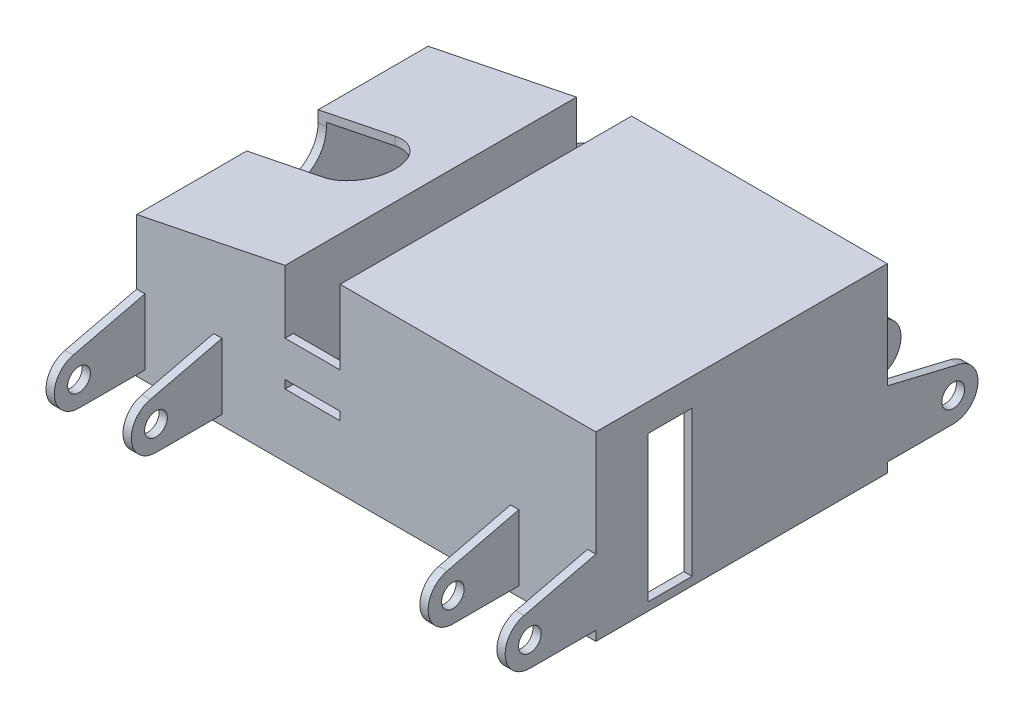
SolidWorks part; units mm, degrees
material "AISI 1020"
ref_plane "Front Plane" through (0, 0, 0) normal (0, 0, 1) x (1, 0, 0)
ref_plane "Top Plane" through (0, 0, 0) normal (0, 1, 0) x (1, 0, 0)
ref_plane "Right Plane" through (0, 0, 0) normal (1, 0, 0) x (0, 0, -1)
sketch "Sketch1" plane through (0, 0, 0) normal (0, 0, 1) x (1, 0, 0)
  line L0 (0, 60) -> (0, -3)
  line L1 (3, -3) -> (0, -3)
  line L2 (3, 63) -> (3, -3)
  line L3 (-87, 60) -> (-87, -3)
  line L4 (-87, -3) -> (-90, -3)
  line L5 (-90, -3) -> (-90, 17)
  line L6 (-90, 20) -> (-110.0009, 20)
  line L7 (-161, 45.5471) -> (-161, -3)
  line L8 (-113, 17) -> (-90, 17)
  line L9 (-161, -3) -> (-164, -3)
  line L11 (-110.0331, 58.9392) -> (-110.0009, 20)
  line L12 (-110.0331, 58.9392) -> (-164, 48)
  line L14 (-113, 55.2768) -> (-161, 45.5471)
  line L15 (-164, -3) -> (-164, 48)
  line L62 (-90, 63) -> (-90, 20)
  line L134 (-113, 55.2768) -> (-113, 17)
  line L139 (-87, 60) -> (0, 60)
  line L143 (3, 63) -> (-90, 63)
extrude "Boss-Extrude1" add sketch "Sketch1" along normal blind 100
sketch "Sketch2" plane through (0, 0, 100) normal (0, 0, 1) x (1, 0, 0)
  line L18 (-164, -3) -> (3, -3)
  line L19 (-164, 48) -> (-110.0331, 58.9392)
  line L21 (-110.0009, 20) -> (-110.0331, 58.9392) construction
  line L22 (-110.0141, 36) -> (-90, 36)
  line L23 (-90, 63) -> (-90, 20) construction
  line L24 (-90, 36) -> (-90, 63)
  line L25 (-110.0331, 58.9392) -> (-110.0141, 36)
  line L36 (3, 63) -> (-90, 63)
  line L37 (-90, 63) -> (-90, 20)
  line L38 (-90, 20) -> (-110.0009, 20)
  line L39 (-110.0009, 20) -> (-110.0331, 58.9392)
  line L40 (-110.0331, 58.9392) -> (-164, 48)
  line L41 (-164, 48) -> (-164, -3)
  line L42 (-164, -3) -> (-161, -3)
  line L43 (-161, -3) -> (-161, 45.5471)
  line L44 (-161, 45.5471) -> (-113, 55.2768)
  line L45 (-113, 55.2768) -> (-113, 17)
  line L46 (-113, 17) -> (-90, 17)
  line L47 (-90, 17) -> (-90, -3)
  line L48 (-90, -3) -> (-87, -3)
  line L49 (-87, -3) -> (-87, 60)
  line L50 (-87, 60) -> (0, 60)
  line L51 (0, 60) -> (0, -3)
  line L52 (0, -3) -> (3, -3)
  line L53 (3, -3) -> (3, 63)
  line L54 (3, 63) -> (-90, 63)
  line L59 (-164, 48) -> (-164, -3)
  line L71 (3, -3) -> (3, 63)
  dimension "D1" = 0
extrude "Boss-Extrude2" add sketch "Sketch2" along normal blind 3
sketch "Sketch4" plane through (0, -3, 0) normal (0, -1, 0) x (1, 0, 0)
  line L0 (-90, 69) -> (-90, 100) construction
  line L7 (-90, 100) -> (-90, 0) construction
  line L8 (-90, 69) -> (-161, 69)
  line L9 (-161, 100) -> (-161, 0) construction
  line L10 (-161, 69) -> (-161, 66)
  line L11 (-161, 66) -> (-90, 66)
  line L12 (-90, 100) -> (-90, 0) construction
  line L13 (-90, 66) -> (-90, 69)
  dimension "D1" = 31
  dimension "D2" = 3
extrude "Boss-Extrude3" add sketch "Sketch4" against normal up to surface (20 mm away) up to face at (-101.5, 17, 50)
sketch "Sketch6" plane through (0, 17, 0) normal (0, 1, 0) x (1, 0, 0)
  line L0 (-113, -69) -> (-113, -66)
  line L1 (-113, -66) -> (-161, -66)
  line L2 (-161, -66) -> (-113, -66) construction
  line L3 (-161, -66) -> (-161, -69)
  line L4 (-161, -69) -> (-113, -69)
extrude "Boss-Extrude4" add sketch "Sketch6" along normal up to surface (28.5471 mm away)
sketch "Sketch7" plane through (-164, 0, 0) normal (-1, 0, 0) x (0, 0, 1)
  line L0 (50, 48) -> (50, 44) construction
  line L1 (103, 48) -> (0, 48) construction
  line L5 (103, 48) -> (63, 48) construction
  line L6 (51.5, 48) -> (50, 48) construction
  line L7 (37, 44) -> (37, 57)
  line L8 (37, 57) -> (63, 57)
  line L9 (63, 57) -> (63, 44)
  line L10 (62.3693, 48) -> (51.5, 48) construction
  arc A1 (37, 44) -> (63, 44) centre (50, 44) ccw
extrude "Cut-Extrude1" cut sketch "Sketch7" against normal blind 3
sketch "Sketch8" plane through (0, 0, 66) normal (0, 0, -1) x (-1, 0, 0)
  line L0 (161, -3) -> (136, -3) construction
  line L1 (161, -3) -> (90, -3) construction
  line L2 (136, -3) -> (136, 22) construction
  line L3 (136, 22) -> (151.5, 22) construction
  line L4 (151.5, 22) -> (151.5, 37.5) construction
  line L5 (151.5, 22) -> (151.5, 6.5) construction
  line L6 (136, 22) -> (120.5, 22) construction
  line L7 (120.5, 22) -> (120.5, 37.5) construction
  line L8 (120.5, 22) -> (120.5, 6.5) construction
  circle A0 centre (136, 22) radius 2.5
  circle A1 centre (151.5, 37.5) radius 1.7
  circle A2 centre (120.5, 37.5) radius 1.7
  circle A3 centre (151.5, 6.5) radius 1.7
  circle A4 centre (120.5, 6.5) radius 1.7
extrude "Cut-Extrude2" cut sketch "Sketch8" against normal blind 3
sketch "Sketch9" plane through (-87, 0, 0) normal (1, 0, 0) x (0, 0, -1)
  line L0 (0, -3) -> (-31, -3) construction
  line L1 (-100, -3) -> (0, -3) construction
  line L2 (-31, -3) -> (-31, 29.5) construction
  line L3 (-31, 29.5) -> (-7.43, 29.5) construction
  line L4 (-7.43, 29.5) -> (-7.43, 5.93) construction
  line L5 (-7.43, 29.5) -> (-7.43, 53.07) construction
  line L6 (-31, 29.5) -> (-54.57, 29.5) construction
  line L7 (-54.57, 29.5) -> (-54.57, 53.07) construction
  line L8 (-54.57, 29.5) -> (-54.57, 5.93) construction
  circle A0 centre (-31, 29.5) radius 3.2
  circle A1 centre (-7.43, 53.07) radius 2.5
  circle A2 centre (-7.43, 5.93) radius 2.5
  circle A3 centre (-54.57, 53.07) radius 2.5
  circle A4 centre (-54.57, 5.93) radius 2.5
  dimension "D1" = 32.5
extrude "Cut-Extrude3" cut sketch "Sketch9" against normal blind 3
sketch "Sketch10" plane through (0, 0, 66) normal (0, 0, -1) x (-1, 0, 0)
  circle A0 centre (99.5, 6.5) radius 1.7
extrude "Cut-Extrude4" cut sketch "Sketch10" against normal blind 3
sketch "Sketch13" plane through (-90, 0, 0) normal (-1, 0, 0) x (0, 0, 1)
  line L0 (78.5, 6.43) -> (78.5, -3) construction
  line L1 (100, -3) -> (0, -3) construction
  line L2 (78.5, 6.43) -> (94.5, 6.43) construction
  circle A0 centre (94.5, 6.43) radius 2.5
extrude "Cut-Extrude6" cut sketch "Sketch13" against normal blind 3
sketch "Sketch14" plane through (0, 0, 0) normal (0, 0, -1) x (-1, 0, 0)
  line L0 (-3, 63) -> (-3, -3)
  line L1 (-3, -3) -> (164, -3)
  line L2 (164, -3) -> (164, 48)
  line L3 (164, 48) -> (110.0331, 58.9392)
  line L4 (110.0331, 58.9392) -> (110.0141, 36)
  line L5 (110.0141, 36) -> (90, 36)
  line L6 (90, 36) -> (90, 63)
  line L7 (90, 63) -> (-3, 63)
extrude "Boss-Extrude5" add sketch "Sketch14" along normal blind 3
sketch "Sketch15" plane through (0, -3, 0) normal (0, -1, 0) x (1, 0, 0)
  line L0 (-161, 100) -> (-159, 100) construction
  line L1 (-161, 100) -> (-113, 100) construction
  line L2 (-159, 100) -> (-159, 98) construction
  line L3 (-154, 98) -> (-154, 100)
  line L4 (-161, 100) -> (-90, 100) construction
  line L5 (-159, 93) -> (-161, 93)
  line L6 (-161, 100) -> (-161, 69) construction
  line L7 (-161, 93) -> (-161, 100)
  line L8 (-161, 100) -> (-154, 100)
  line L9 (0, 100) -> (-2, 100) construction
  line L10 (-87, 100) -> (0, 100) construction
  line L11 (-2, 100) -> (-2, 98) construction
  line L12 (-7, 98) -> (-7, 100)
  line L13 (-2, 93) -> (0, 93)
  line L14 (0, 100) -> (0, 0) construction
  line L15 (-7, 100) -> (0, 100)
  line L16 (0, 100) -> (0, 93)
  line L17 (-161, 0) -> (-159, 0) construction
  line L18 (-161, 0) -> (-113, 0) construction
  line L19 (-159, 0) -> (-159, 2) construction
  line L20 (-159, 7) -> (-161, 7)
  line L21 (-161, 66) -> (-161, 0) construction
  line L22 (-154, 2) -> (-154, 0)
  line L23 (-90, 0) -> (-161, 0) construction
  line L24 (-161, 7) -> (-161, 0)
  line L25 (-161, 0) -> (-154, 0)
  line L26 (0, 0) -> (-2, 0) construction
  line L27 (-87, 0) -> (0, 0) construction
  line L28 (-2, 0) -> (-2, 2) construction
  line L29 (-7, 2) -> (-7, 0)
  line L30 (-2, 7) -> (0, 7)
  line L31 (0, 100) -> (0, 0) construction
  line L32 (0, 7) -> (0, 0)
  line L33 (0, 0) -> (-7, 0)
  circle A0 centre (-159, 98) radius 2
  arc A1 (-159, 93) -> (-154, 98) centre (-159, 98) ccw
  circle A2 centre (-159, 98) radius 5 construction
  circle A3 centre (-2, 98) radius 2
  arc A4 (-7, 98) -> (-2, 93) centre (-2, 98) ccw
  circle A5 centre (-2, 98) radius 5 construction
  circle A6 centre (-159, 2) radius 2
  arc A7 (-154, 2) -> (-159, 7) centre (-159, 2) ccw
  circle A8 centre (-159, 2) radius 5 construction
  circle A9 centre (-2, 2) radius 2
  arc A10 (-2, 7) -> (-7, 2) centre (-2, 2) ccw
  circle A11 centre (-2, 2) radius 5 construction
  line M15 (0, 0) -> (-87, 0)
  line M17 (-87, 100) -> (0, 100)
  line M18 (0, 100) -> (0, 0)
  line M19 (-161, 0) -> (-161, 66)
  line M22 (-90, 0) -> (-161, 0)
  line M24 (-161, 69) -> (-161, 100)
  line M25 (-161, 100) -> (-90, 100)
  dimension "D1" = 3
  dimension "D2" = 3
  dimension "D3" = 3
  dimension "D4" = 3
extrude "Boss-Extrude6" add sketch "Sketch15" against normal blind 5 contours L5 A1 L3 L8 A0 M24 | A0 L7 M25 | L12 A4 L13 L16 A3 M17 | A3 L15 M18 | L30 A10 L29 L33 A9 M18 | A9 L32 M15 | L22 A7 L20 L24 A6 M22 | A6 L25 M19
sketch "Sketch19" plane through (0, 63, 0) normal (0, 1, 0) x (1, 0, 0)
  line L0 (-161, -50) -> (-136, -50) construction
  line L1 (-161, -63) -> (-161, -37) construction
  line L2 (-136, -37) -> (-164, -37)
  line L3 (-164, -37) -> (-164, -63)
  line L4 (-164, -63) -> (-136, -63)
  arc A0 (-136, -63) -> (-136, -37) centre (-136, -50) ccw
extrude "Cut-Extrude8" cut sketch "Sketch19" against normal blind 18
sketch "Sketch20" plane through (0, 0, 100) normal (0, 0, -1) x (-1, 0, 0)
  line L0 (90, 36) -> (90, 20) construction
  line L1 (110.0009, 20) -> (90, 20)
  line L2 (110.0009, 20) -> (110.0009, 23)
  line L3 (110.0009, 23) -> (90, 23)
  line L4 (90, 20) -> (90, 23)
  dimension "D1" = 3
extrude "Cut-Extrude9" cut sketch "Sketch20" against normal blind 3
sketch "Sketch21" plane through (0, 0, 0) normal (0, 0, 1) x (1, 0, 0)
  line L0 (-90, 36) -> (-90, 20) construction
  line L1 (-110.0009, 20) -> (-90, 20)
  line L2 (-110.0009, 20) -> (-110.0009, 23)
  line L3 (-110.0009, 23) -> (-90, 23)
  line L4 (-90, 20) -> (-90, 23)
  dimension "D1" = 3
extrude "Cut-Extrude10" cut sketch "Sketch21" against normal blind 3
sketch "Sketch22" plane through (-164, 0, 0) normal (-1, 0, 0) x (0, 0, 1)
  line L0 (103, -3) -> (103, 9.5) construction
  line L1 (103, 48) -> (103, -3) construction
  line L2 (103, 0.5) -> (103, 24.5)
  line L3 (127, 0.5) -> (103, 0.5)
  line L4 (103, 24.5) -> (129.0954, 18.2527)
  line L5 (50, -3) -> (50, 28.093) construction
  line L6 (103, -3) -> (-3, -3) construction
  line L7 (-3, -3) -> (-3, 9.5) construction
  line L8 (-3, 24.5) -> (-29.0954, 18.2527)
  line L9 (-27, 0.5) -> (-3, 0.5)
  line L10 (-3, 0.5) -> (-3, 24.5)
  circle A2 centre (127, 9.5) radius 4.125
  arc A3 (127, 0.5) -> (129.0954, 18.2527) centre (127, 9.5) ccw
  arc A4 (-27, 0.5) -> (-29.0954, 18.2527) centre (-27, 9.5) cw
  circle A5 centre (-27, 9.5) radius 4.125
  dimension "D1" = 12.5
extrude "Boss-Extrude7" add sketch "Sketch22" against normal blind 3
pattern_linear "LPattern1" count 2 spacing 28 along (1, 0, 0) of "Boss-Extrude7"
pattern_linear "LPattern2" count 2 spacing 164 along (1, 0, 0) of "Boss-Extrude7"
pattern_linear "LPattern3" count 2 spacing 136 along (1, 0, 0) of "Boss-Extrude7"
sketch "Sketch23" plane through (3, 0, 0) normal (1, 0, 0) x (0, 0, -1)
  line L0 (-103, -3) -> (-84, -3) construction
  line L1 (-103, -3) -> (3, -3) construction
  line L2 (-84, -3) -> (-84, 0) construction
  line L4 (-84, 0) -> (-68, 0)
  line L5 (-84, 0) -> (-84, 53)
  line L6 (-84, 53) -> (-68, 53)
  line L7 (-68, 0) -> (-68, 53)
  dimension "D1" = 16
  dimension "D2" = 53
  dimension "D3" = 3
extrude "Cut-Extrude11" cut sketch "Sketch23" against normal blind 3
